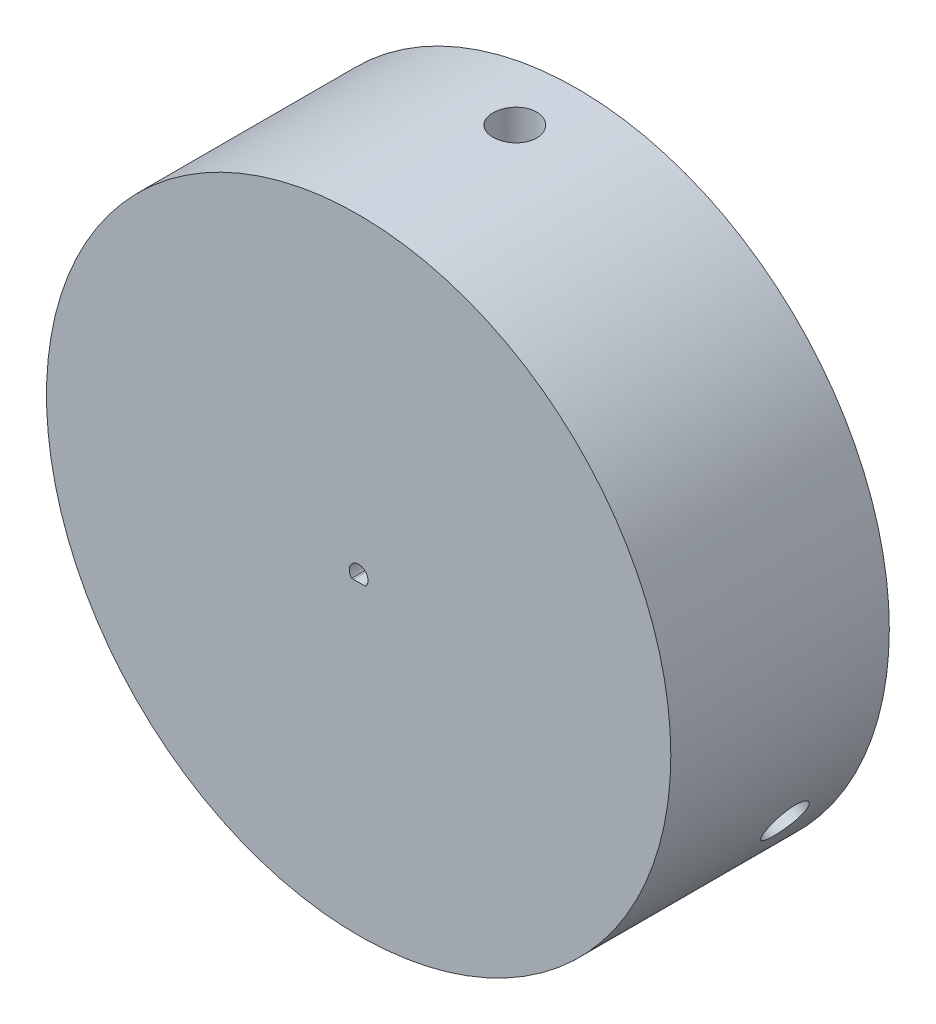
SolidWorks part; units mm, degrees
ref_plane "Front Plane" through (0, 0, 0) normal (0, 0, 1) x (1, 0, 0)
ref_plane "Top Plane" through (0, 0, 0) normal (0, 1, 0) x (1, 0, 0)
ref_plane "Right Plane" through (0, 0, 0) normal (1, 0, 0) x (0, 0, -1)
sketch "Sketch2" plane through (0, 0, 0) normal (0, 0, 1) x (1, 0, 0)
  circle A0 centre (0, 0) radius 50
  dimension "D1" = 100
extrude "Boss-Extrude1" add sketch "Sketch2" along normal blind 35
sketch "Sketch3" plane through (0, 0, 0) normal (0, 0, -1) x (-1, 0, 0)
  line L0 (-4, 39) -> (-4, 4)
  line L1 (-4, 4) -> (4, 4)
  line L2 (4, 4) -> (4, 39)
  line L3 (4, 39) -> (-4, 39)
  line L4 (31.775, -22.9641) -> (35.775, -16.0359)
  line L5 (35.775, -16.0359) -> (5.4641, 1.4641)
  line L6 (5.4641, 1.4641) -> (1.4641, -5.4641)
  line L7 (1.4641, -5.4641) -> (31.775, -22.9641)
  line L8 (-35.775, -16.0359) -> (-31.775, -22.9641)
  line L9 (-31.775, -22.9641) -> (-1.4641, -5.4641)
  line L10 (-1.4641, -5.4641) -> (-5.4641, 1.4641)
  line L11 (-5.4641, 1.4641) -> (-35.775, -16.0359)
  point P16 (0, 0)
  dimension "D1" = 4
  dimension "D2" = 8
  dimension "D3" = 35
  dimension "D4" = 4
  dimension "D5" = 3
extrude "Cut-Extrude1" cut sketch "Sketch3" against normal blind 20 contours L3 L0 L1 L2 | L8 L9 L10 L11 | L4 L5 L6 L7
sketch "Sketch4" plane through (-3.4641, -2, 0) normal (-0.866, -0.5, 0) x (0, 0, 1)
  line L0 (20, 4) -> (20, -4) construction
  line L1 (0, 4) -> (0, -4) construction
  line L2 (20, 4) -> (20, -4)
  line L3 (0, 4) -> (0, -4)
  circle A0 centre (10, 0) radius 3.5
  dimension "D1" = 7
  dimension "D2" = 10
  dimension "D3" = 8
  dimension "D4" = 4
extrude "Cut-Extrude2" cut sketch "Sketch4" along normal blind 80 contours A0
sketch "Sketch5" plane through (0, 4, 0) normal (0, 1, 0) x (1, 0, 0)
  line L0 (4, 0) -> (-4, 0) construction
  line L1 (4, -20) -> (-4, -20) construction
  line L2 (4, 0) -> (-4, 0)
  line L3 (4, -20) -> (-4, -20)
  circle A0 centre (0, -10) radius 3.5
  dimension "D1" = 7
  dimension "D2" = 10
extrude "Cut-Extrude3" cut sketch "Sketch5" along normal blind 50 contours A0
sketch "Sketch6" plane through (3.4641, -2, 0) normal (0.866, -0.5, 0) x (0, 0, -1)
  line L0 (-20, -4) -> (-20, 4) construction
  line L1 (0, -4) -> (0, 4) construction
  line L2 (-20, -4) -> (-20, 4)
  line L3 (0, -4) -> (0, 4)
  circle A0 centre (-10, 0) radius 3.5
  point P6 (-20, 0)
  dimension "D1" = 7
  dimension "D2" = 10
  dimension "D3" = 0
extrude "Cut-Extrude4" cut sketch "Sketch6" along normal blind 50 contours A0
sketch "Sketch8" plane through (0, 0, 0) normal (0, 0, -1) x (-1, 0, 0)
  line L0 (-32.9711, -10.8924) -> (-25.9519, -23.0501)
  line L1 (-32.9711, -10.8924) -> (-27.3419, -7.6424)
  line L2 (-27.3419, -7.6424) -> (-20.3227, -19.8001)
  line L3 (-20.3227, -19.8001) -> (-25.9519, -23.0501)
  line L4 (-35.775, -16.0359) -> (-31.775, -22.9641) construction
  line L5 (-35.775, -16.0359) -> (-31.775, -22.9641)
  line L6 (-6.986, 27.5) -> (-6.986, 34)
  line L7 (7.0524, 34) -> (-6.986, 34)
  line L8 (7.0524, 34) -> (7.0524, 27.5)
  line L9 (7.0524, 27.5) -> (-6.986, 27.5)
  line L10 (27.3087, -7.6999) -> (32.9379, -10.9499)
  line L11 (25.9186, -23.1076) -> (32.9379, -10.9499)
  line L12 (25.9186, -23.1076) -> (20.2895, -19.8576)
  line L13 (20.2895, -19.8576) -> (27.3087, -7.6999)
  point P17 (0, 0)
  dimension "D1" = 5
  dimension "D2" = 6.5
  dimension "D3" = 14.0384
  dimension "D4" = 3
extrude "Cut-Extrude5" cut sketch "Sketch8" against normal blind 15.5 contours L0 L3 L2 L1 | L9 L6 L7 L8 | L11 L10 L13 L12
sketch "Sketch11" plane through (0, 0, 20) normal (0, 0, -1) x (-1, 0, 0)
  line L0 (-4, 34) -> (4, 34)
  line L1 (4, 27.5) -> (4, 34) construction
  line L2 (4, 4) -> (4, 39) construction
  line L3 (4, 34) -> (4, 27.5)
  line L4 (4, 27.5) -> (-4, 27.5)
  line L5 (-4, 27.5) -> (-4, 34)
  line L6 (25.8157, -10.2859) -> (31.4449, -13.5359)
  line L7 (31.4449, -13.5359) -> (27.4449, -20.4641)
  line L8 (27.4449, -20.4641) -> (21.8157, -17.2141)
  line L9 (21.8157, -17.2141) -> (25.8157, -10.2859)
  line L10 (-21.8157, -17.2141) -> (-27.4449, -20.4641)
  line L11 (-27.4449, -20.4641) -> (-31.4449, -13.5359)
  line L12 (-31.4449, -13.5359) -> (-25.8157, -10.2859)
  line L13 (-25.8157, -10.2859) -> (-21.8157, -17.2141)
  point P21 (0, 0)
  dimension "D1" = 3
extrude "Boss-Extrude2" add sketch "Sketch11" along normal blind 4.5
sketch "Sketch12" plane through (0, 0, 15.5) normal (0, 0, -1) x (-1, 0, 0)
  line L0 (-6.986, 32.1) -> (7.0524, 32.1)
  line L1 (-6.986, 27.5) -> (-6.986, 34) construction
  line L2 (7.0524, 34) -> (7.0524, 27.5) construction
  line L3 (7.0524, 34) -> (4, 34) construction
  line L5 (-4, 34) -> (-6.986, 34) construction
  line L6 (7.0524, 34) -> (4, 34)
  line L8 (-4, 34) -> (-6.986, 34)
  line L9 (-6.986, 32.1) -> (-6.986, 34)
  line L10 (7.0524, 32.1) -> (7.0524, 34)
  line L11 (4, 34) -> (4, 39) construction
  line L12 (4, 39) -> (-4, 39) construction
  line L13 (-4, 39) -> (-4, 34) construction
  line L14 (4, 34) -> (4, 39)
  line L15 (4, 39) -> (-4, 39)
  line L16 (-4, 39) -> (-4, 34)
  line L17 (25.9186, -23.1076) -> (27.4449, -20.4641)
  line L18 (27.4449, -20.4641) -> (31.775, -22.9641)
  line L19 (31.775, -22.9641) -> (35.775, -16.0359)
  line L20 (35.775, -16.0359) -> (31.4449, -13.5359)
  line L21 (31.4449, -13.5359) -> (32.9379, -10.9499)
  line L22 (31.2924, -9.9999) -> (32.9379, -10.9499)
  line L23 (31.2924, -9.9999) -> (24.2732, -22.1576)
  line L24 (24.2732, -22.1576) -> (25.9186, -23.1076)
  line L25 (-32.9711, -10.8924) -> (-31.4449, -13.5359)
  line L26 (-31.4449, -13.5359) -> (-35.775, -16.0359)
  line L27 (-35.775, -16.0359) -> (-31.775, -22.9641)
  line L28 (-31.775, -22.9641) -> (-27.4449, -20.4641)
  line L29 (-27.4449, -20.4641) -> (-25.9519, -23.0501)
  line L30 (-24.3064, -22.1001) -> (-25.9519, -23.0501)
  line L31 (-24.3064, -22.1001) -> (-31.3256, -9.9424)
  line L32 (-31.3256, -9.9424) -> (-32.9711, -10.8924)
  point P30 (0, 0)
  dimension "D1" = 1.9
  dimension "D2" = 3
extrude "Boss-Extrude3" add sketch "Sketch12" along normal up to surface (15.5 mm away) up to face at (50, 0, 0)
sketch "Sketch13" plane through (0, 34, 0) normal (0, 1, 0) x (1, 0, 0)
  circle A0 centre (0, -10) radius 3.5 construction
  circle A1 centre (0, -10) radius 3.5
sketch "Sketch14" plane through (33.775, -19.5, 0) normal (0.866, -0.5, 0) x (0, 0, -1)
  circle A0 centre (-10, 0) radius 3.5 construction
  circle A1 centre (-10, 0) radius 3.5
sketch "Sketch15" plane through (-33.775, -19.5, 0) normal (-0.866, -0.5, 0) x (0, 0, 1)
  circle A0 centre (10, 0) radius 3.5 construction
  circle A1 centre (10, 0) radius 3.5
sketch "Sketch17" plane through (0, 0, 0) normal (0, 0, -1) x (-1, 0, 0)
  line L0 (-5.8428, 32.8975) -> (-5.8428, 43.5095)
  line L5 (-5.8428, 43.5095) -> (5.7278, 43.5095)
  line L6 (5.7278, 43.5095) -> (5.7548, 32.8975)
  line L10 (-5.8428, 32.8975) -> (5.7548, 32.8975)
  line L11 (31.4114, -11.3887) -> (25.6127, -21.4325)
  line L12 (34.8164, -26.7152) -> (25.6127, -21.4325)
  line L13 (40.6018, -16.6948) -> (34.8164, -26.7152)
  line L14 (31.4114, -11.3887) -> (40.6018, -16.6948)
  line L15 (-25.5686, -21.5087) -> (-31.3674, -11.465)
  line L16 (-40.5443, -16.7943) -> (-31.3674, -11.465)
  line L17 (-34.759, -26.8148) -> (-40.5443, -16.7943)
  line L18 (-25.5686, -21.5087) -> (-34.759, -26.8148)
  point P22 (0, 0)
  dimension "D1" = 3
extrude "Boss-Extrude4" add sketch "Sketch17" against normal up to surface (35 mm away) up to face at (50, 0, 35)
sketch "Sketch18" plane through (-37.6804, -21.7548, 0) normal (-0.866, -0.5, 0) x (0, 0, 1)
  circle A0 centre (10, 0) radius 3.5 construction
  circle A1 centre (10, 0) radius 3.5
extrude "Cut-Extrude9" cut sketch "Sketch18" against normal mid plane 50
sketch "Sketch19" plane through (37.6804, -21.7548, 0) normal (0.866, -0.5, 0) x (0, 0, -1)
  circle A0 centre (-10, 0) radius 3.5 construction
  circle A1 centre (-10, 0) radius 3.5
extrude "Cut-Extrude10" cut sketch "Sketch19" against normal mid plane 50
sketch "Sketch20" plane through (0, 43.5095, 0) normal (0, 1, 0) x (1, 0, 0)
  circle A0 centre (0, -10) radius 3.5 construction
  circle A1 centre (0, -10) radius 3.5
extrude "Cut-Extrude11" cut sketch "Sketch20" against normal mid plane 50
sketch "Sketch21" plane through (0, 0, 0) normal (0, 0, -1) x (-1, 0, 0)
  line L1 (4, 4) -> (4, 27.5) construction
  line L3 (4, 22.4) -> (9.1, 22.4)
  line L4 (4, 4) -> (4, 27.5) construction
  line L6 (4, 4) -> (4, 22.4)
  line L8 (4, 4) -> (4, 22.4)
  line L9 (4, 22.4) -> (9.1, 22.4)
  line L10 (4, 4) -> (9.1, 4)
  line L11 (9.1, 22.4) -> (9.1, 4)
  line L12 (7.0524, 27.5) -> (4, 27.5) construction
  dimension "D1" = 18.4
  dimension "D2" = 5.1
  dimension "D3" = 5.1
extrude "Cut-Extrude12" cut sketch "Sketch21" against normal blind 13
sketch "Sketch22" plane through (0, 0, 0) normal (0, 0, -1) x (-1, 0, 0)
  line L0 (4, 4) -> (4, 17.3)
  line L1 (4, 4) -> (4, 27.5) construction
  line L2 (4, 17.3) -> (9.1, 17.3)
  line L3 (9.1, 22.4) -> (9.1, 4) construction
  line L4 (9.1, 17.3) -> (9.1, 4)
  line L5 (9.1, 4) -> (4, 4)
  line L6 (4, 22.4) -> (9.1, 22.4) construction
  line L7 (-1.0859, -9.8808) -> (1.4641, -5.4641)
  line L8 (1.4641, -5.4641) -> (12.9822, -12.1141)
  line L9 (12.9822, -12.1141) -> (10.4322, -16.5308)
  line L10 (10.4322, -16.5308) -> (-1.0859, -9.8808)
  line L11 (-8.0141, 5.8808) -> (-5.4641, 1.4641)
  line L12 (-5.4641, 1.4641) -> (-16.9822, -5.1859)
  line L13 (-16.9822, -5.1859) -> (-19.5322, -0.7692)
  line L14 (-19.5322, -0.7692) -> (-8.0141, 5.8808)
  point P23 (0, 0)
  dimension "D1" = 5.1
  dimension "D2" = 3
sketch "Sketch23" plane through (0, 0, 0) normal (0, 0, -1) x (-1, 0, 0)
  line L0 (4, 4) -> (4, 22.4)
  line L1 (4, 22.4) -> (9.1, 22.4)
  line L2 (9.1, 22.4) -> (9.1, 4)
  line L3 (9.1, 4) -> (4, 4)
  line L4 (-1.0859, -9.8808) -> (1.4641, -5.4641)
  line L5 (1.4641, -5.4641) -> (17.399, -14.6641)
  line L6 (17.399, -14.6641) -> (14.849, -19.0808)
  line L7 (14.849, -19.0808) -> (-1.0859, -9.8808)
  line L8 (-8.0141, 5.8808) -> (-5.4641, 1.4641)
  line L9 (-5.4641, 1.4641) -> (-21.399, -7.7359)
  line L10 (-21.399, -7.7359) -> (-23.949, -3.3192)
  line L11 (-23.949, -3.3192) -> (-8.0141, 5.8808)
  point P18 (0, 0)
  dimension "D1" = 3
extrude "Cut-Extrude13" cut sketch "Sketch23" against normal blind 13
extrude "Boss-Extrude5" add sketch "Sketch22" against normal blind 7.9
sketch "Sketch24" plane through (0, 0, 35) normal (0, 0, 1) x (1, 0, 0)
  line L0 (0.8316, -1) -> (1.1181, -0.9999)
  line L1 (-1.1181, -0.9999) -> (-0.8313, -1)
  line L2 (0.8316, -1) -> (-0.8313, -1)
  arc A0 (1.1181, -0.9999) -> (-1.5, 0) centre (0, 0) ccw
  arc A1 (-1.5, 0) -> (-1.1181, -0.9999) centre (0, 0) ccw
  dimension "D1" = 0
extrude "Cut-Extrude14" cut sketch "Sketch24" against normal blind 8.5
sketch "Sketch25" plane through (0, 0, 0) normal (0, 0, -1) x (-1, 0, 0)
  circle A0 centre (0, 0) radius 9
  dimension "D1" = 18
extrude "Cut-Extrude15" cut sketch "Sketch25" against normal up to surface (20 mm away) up to face at (-13.6399, -7.875, 20)
